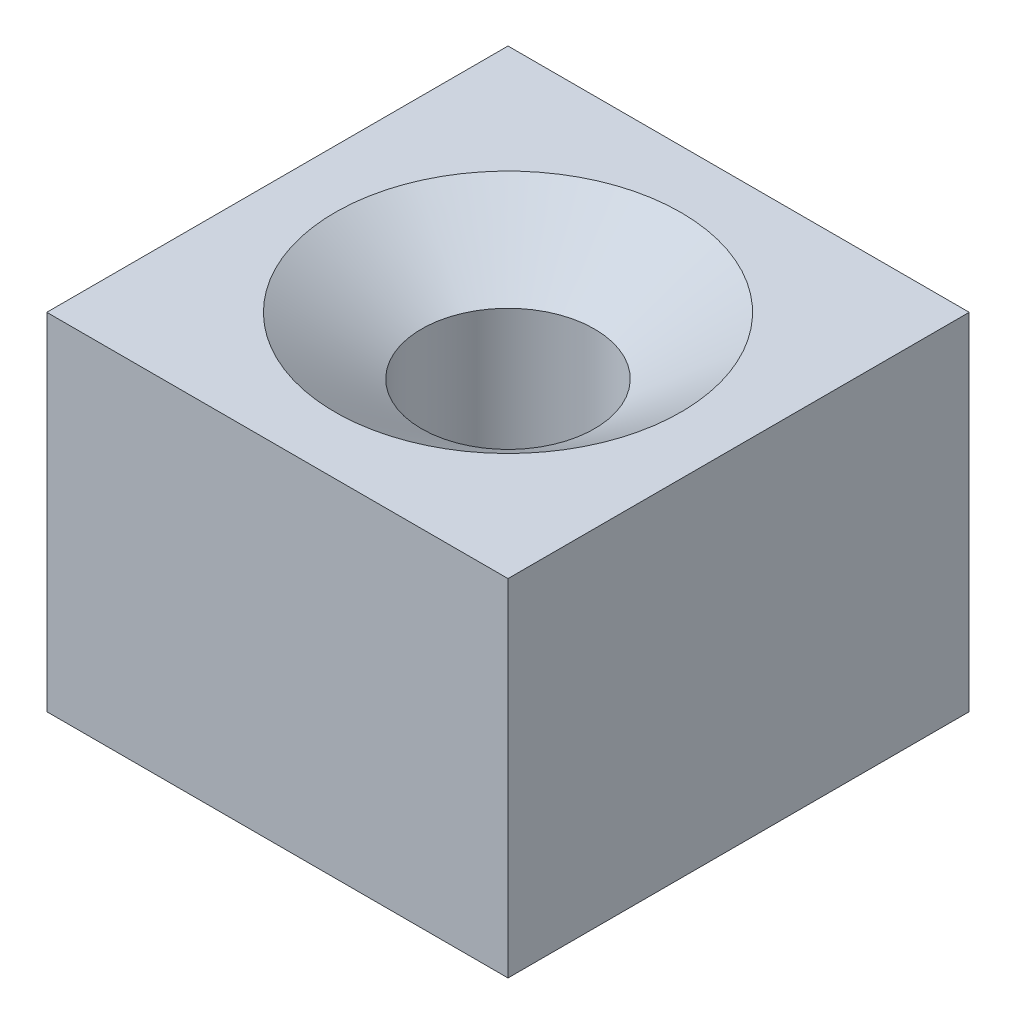
SolidWorks part; units mm, degrees
ref_plane "Front Plane" through (0, 0, 0) normal (0, 0, 1) x (1, 0, 0)
ref_plane "Top Plane" through (0, 0, 0) normal (0, 1, 0) x (1, 0, 0)
ref_plane "Right Plane" through (0, 0, 0) normal (1, 0, 0) x (0, 0, -1)
sketch "Sketch1" plane through (0, 0, 0) normal (0, 1, 0) x (1, 0, 0)
  line L1 (-40, -40) -> (40, -40)
  line L2 (-40, -40) -> (-40, 40)
  line L3 (-40, 40) -> (40, 40)
  line L4 (40, -40) -> (40, 40)
  line L5 (-40, -40) -> (40, 40) construction
  line L6 (-40, 40) -> (40, -40) construction
  point P0 (0, 0)
  dimension "D1" = 80
  dimension "D2" = 80
extrude "Boss-Extrude1" add sketch "Sketch1" along normal blind 60
sketch "Sketch2" plane through (0, 0, 0) normal (0, 0, 1) x (1, 0, 0)
  line L0 (40, 60) -> (0, 60) construction
  line L1 (-40, 60) -> (40, 60) construction
  line L2 (0, 60) -> (-30, 60)
  line L3 (-30, 60) -> (-15, 50)
  line L4 (-15, 50) -> (-15, 10)
  line L5 (-15, 10) -> (0, 10)
  line L6 (0, 10) -> (0, 60)
  point P4 (40, 60)
  dimension "D1" = 50
  dimension "D2" = 10
  dimension "D3" = 15
  dimension "D4" = 40
  dimension "D5" = 30
revolve "Cut-Revolve1" cut sketch "Sketch2" angle 360 about L6
